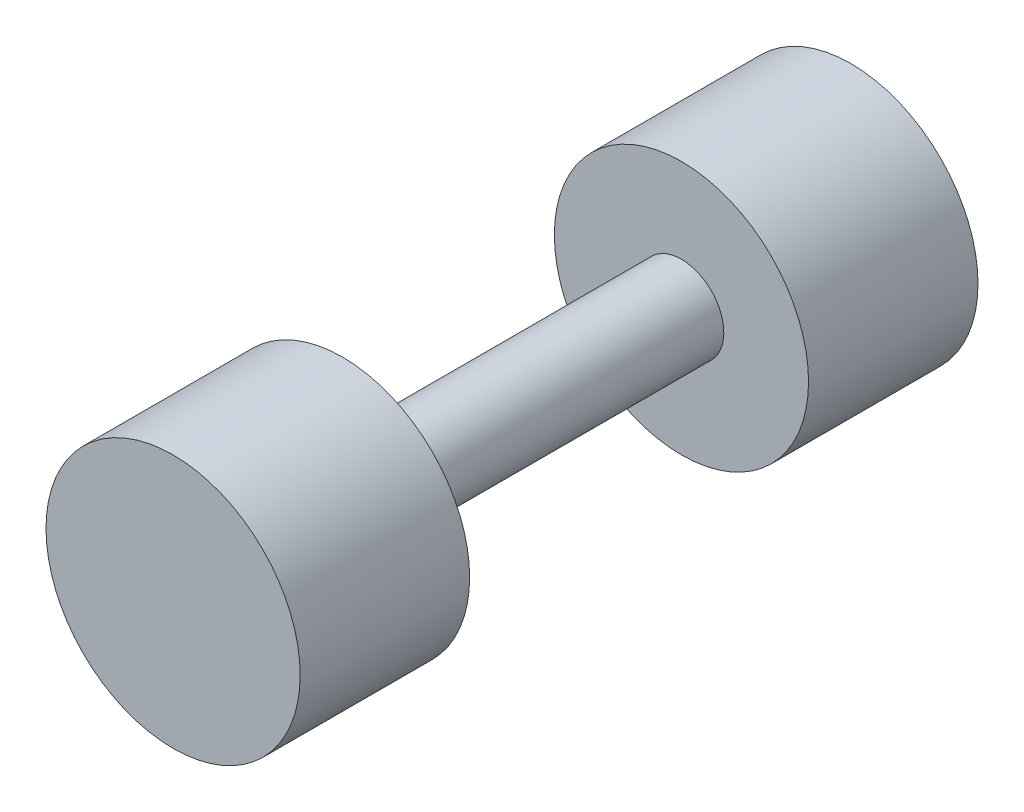
SolidWorks part; units mm, degrees
material "6061 Alloy"
ref_plane "Front Plane" through (0, 0, 0) normal (0, 0, 1) x (1, 0, 0)
ref_plane "Top Plane" through (0, 0, 0) normal (0, 1, 0) x (1, 0, 0)
ref_plane "Right Plane" through (0, 0, 0) normal (1, 0, 0) x (0, 0, -1)
sketch "Sketch1" plane through (0, 0, 0) normal (1, 0, 0) x (0, 0, -1)
  line L0 (50.8, 0) -> (-50.8, 0)
  line L1 (-50.8, 0) -> (-50.8, 19.05)
  line L2 (-50.8, 19.05) -> (-25.4, 19.05)
  line L3 (-25.4, 19.05) -> (-25.4, 6.35)
  line L4 (-25.4, 6.35) -> (25.4, 6.35)
  line L5 (25.4, 6.35) -> (25.4, 19.05)
  line L6 (25.4, 19.05) -> (50.8, 19.05)
  line L7 (50.8, 19.05) -> (50.8, 0)
  point P4 (0, 0)
  dimension "D1" = 25.4
  dimension "D2" = 19.05
  dimension "D3" = 6.35
  dimension "D4" = 101.6
revolve "Revolve1" add sketch "Sketch1" angle 360 about L0
